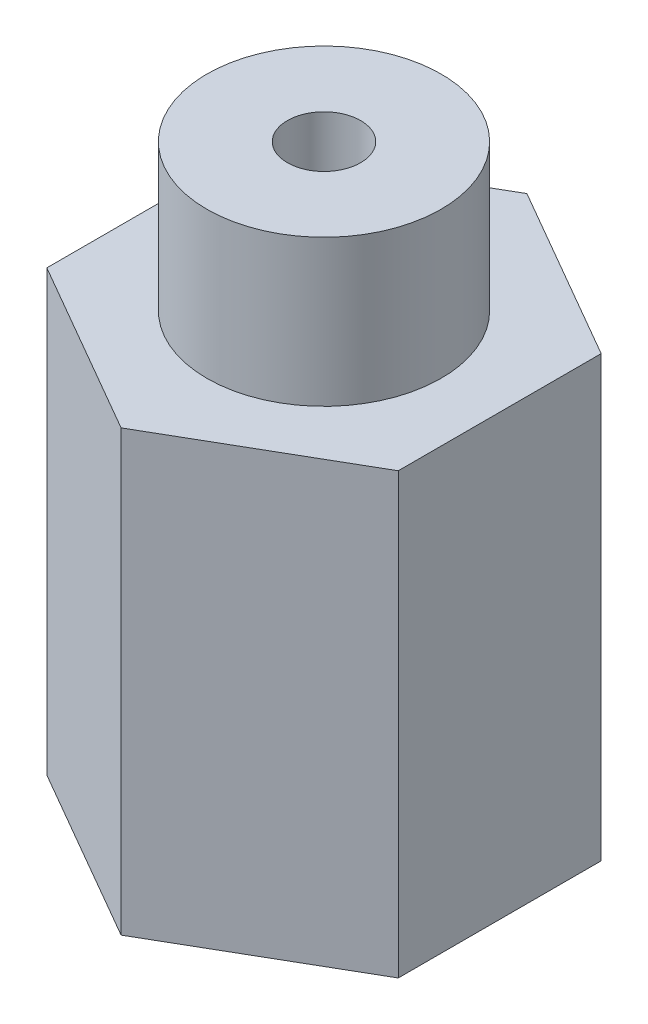
SolidWorks part; units mm, degrees
ref_plane "Спереди" through (0, 0, 0) normal (0, 0, 1) x (1, 0, 0)
ref_plane "Сверху" through (0, 0, 0) normal (0, 1, 0) x (1, 0, 0)
ref_plane "Справа" through (0, 0, 0) normal (1, 0, 0) x (0, 0, -1)
sketch "Эскиз1" plane through (0, 0, 0) normal (0, 1, 0) x (1, 0, 0)
  line L1 (0, 13.8564) -> (-12, 6.9282)
  line L2 (-12, 6.9282) -> (-12, -6.9282)
  line L3 (-12, -6.9282) -> (0, -13.8564)
  line L4 (0, -13.8564) -> (12, -6.9282)
  line L5 (12, -6.9282) -> (12, 6.9282)
  line L6 (12, 6.9282) -> (0, 13.8564)
  circle A0 centre (0, 0) radius 12 construction
extrude "Бобышка-Вытянуть1" add sketch "Эскиз1" along normal blind 40
sketch "Эскиз3" plane through (0, 40, 0) normal (0, 1, 0) x (1, 0, 0)
  circle A0 centre (0, 0) radius 2.5
extrude "Вырез-Вытянуть2" cut sketch "Эскиз3" against normal blind 35
sketch "Эскиз4" plane through (0, 40, 0) normal (0, 1, 0) x (1, 0, 0)
  circle A0 centre (0, 0) radius 8
extrude "Вырез-Вытянуть3" cut sketch "Эскиз4" against normal blind 10 flip side to cut
sketch "Эскиз5" plane through (-6, 0, -10.3923) normal (-0.5, 0, -0.866) x (-0.866, 0, 0.5)
  circle A0 centre (0, 8) radius 5
extrude "Вырез-Вытянуть4" cut sketch "Эскиз5" against normal blind 15
